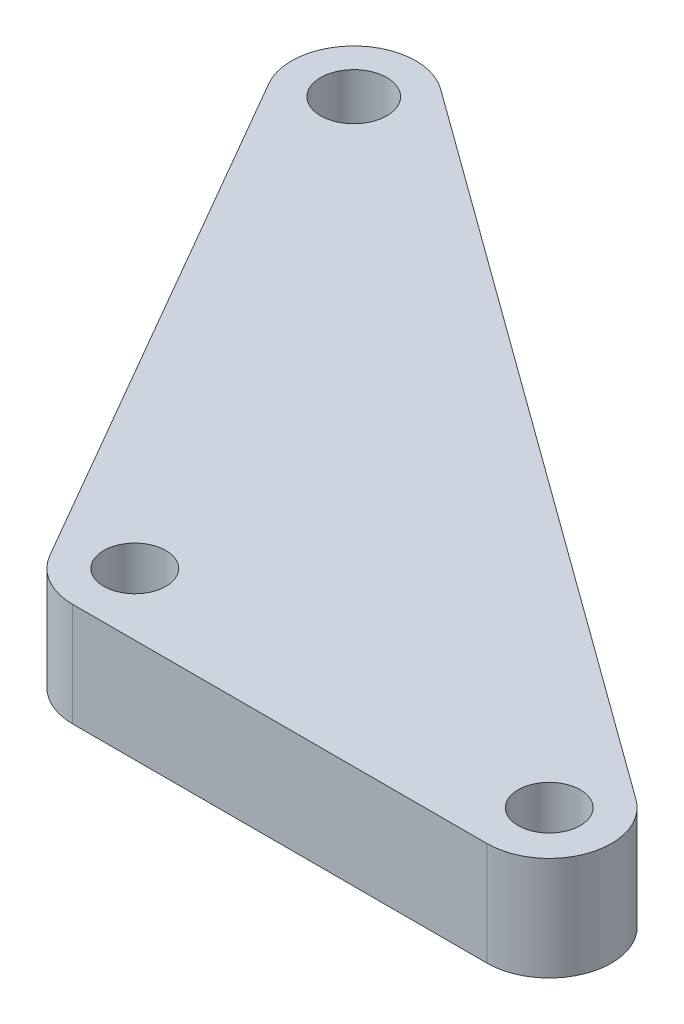
SolidWorks part; units mm, degrees
ref_plane "Front Plane" through (0, 0, 0) normal (0, 0, 1) x (1, 0, 0)
ref_plane "Top Plane" through (0, 0, 0) normal (0, 1, 0) x (1, 0, 0)
ref_plane "Right Plane" through (0, 0, 0) normal (1, 0, 0) x (0, 0, -1)
sketch "Sketch2" plane through (0, 0, 0) normal (0, 1, 0) x (1, 0, 0)
  line L0 (0, 0) -> (0, -25) construction
  line L1 (0, 0) -> (14.4338, -25) construction
  line L2 (14.4338, -25) -> (34.4338, -25) construction
  line L3 (0, 0) -> (34.4338, -25) construction
  line L4 (12.7017, -28) -> (43.6721, -28)
  line L5 (-9.6492, 10.7129) -> (12.7017, -28)
  line L6 (-9.6492, 10.7129) -> (43.6721, -28)
  circle A0 centre (0, 0) radius 1.6
  circle A1 centre (0, 0) radius 3 construction
  circle A2 centre (14.4338, -25) radius 1.5
  circle A3 centre (34.4338, -25) radius 1.5
  circle A4 centre (14.4338, -25) radius 3 construction
  circle A5 centre (34.4338, -25) radius 3 construction
  point P11 (43.6721, -28)
  point P15 (12.7264, -28)
  point P17 (-10.3415, 11.2155)
  point P18 (-9.2962, 10.4566)
  point P19 (-9.3424, 10.1815)
  point P20 (12.5605, -27.7554)
  point P21 (44.263, -28)
  dimension "D1" = 3.2
  dimension "D2" = 6
  dimension "D6" = 3
  dimension "D7" = 3
  dimension "D8" = 6
  dimension "D9" = 6
  dimension "D3" = 25
  dimension "D4" = 30
  dimension "D5" = 20
extrude "Boss-Extrude2" add sketch "Sketch2" along normal blind 5
fillet "Fillet1" radius 3 3 edges at (43.6721, 2.5, 28) (12.7017, 2.5, 28) (-9.6492, 2.5, -10.7129)
